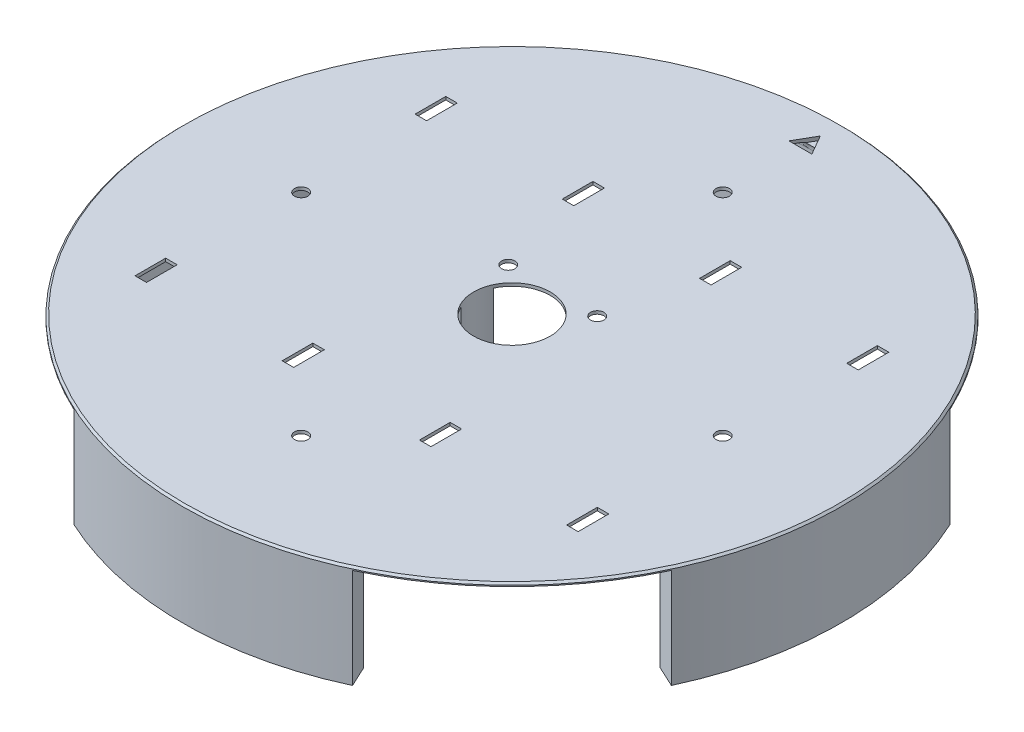
SolidWorks part; units mm, degrees
ref_plane "Ebene vorne" through (0, 0, 0) normal (0, 0, 1) x (1, 0, 0)
ref_plane "Ebene oben" through (0, 0, 0) normal (0, 1, 0) x (1, 0, 0)
ref_plane "Ebene rechts" through (0, 0, 0) normal (1, 0, 0) x (0, 0, -1)
sketch "Skizze1" plane through (0, 0, 0) normal (0, 1, 0) x (1, 0, 0)
  circle A0 centre (0, 0) radius 86
  dimension "D1" = 172
extrude "Aufsatz-Linear austragen1" add sketch "Skizze1" along normal blind 0.8
sketch "Skizze2" plane through (0, 0, 0) normal (0, -1, 0) x (1, 0, 0)
  line L0 (0, 0) -> (0, 86) construction
  line L1 (-36.3452, 77.9425) -> (-33.8095, 72.5046)
  line L2 (0, 0) -> (-36.3452, 77.9425) construction
  line L3 (36.3452, 77.9425) -> (33.8095, 72.5046)
  arc A2 (36.3452, 77.9425) -> (-36.3452, 77.9425) centre (0, 0) ccw
  arc A3 (33.8095, 72.5046) -> (-33.8095, 72.5046) centre (0, 0) ccw
  circle A9 centre (0, 0) radius 86 construction
  dimension "D2" = 6
  dimension "D1" = 25
extrude "Aufsatz-Linear austragen2" add sketch "Skizze2" along normal up to surface (26 mm away)
pattern_circular "Kreismuster1" count 4 over 360 about axis through (0, -99.9325, 0) along (0, 1, 0) of "Aufsatz-Linear austragen2"
sketch "Skizze4" plane through (0, 0, 0) normal (0, -1, 0) x (1, 0, 0)
  circle A0 centre (0, 0) radius 10
extrude "Schnitt-Linear austragen1" cut sketch "Skizze4" against normal up to next
sketch "Skizze7" plane through (0, 0, 0) normal (0, -1, 0) x (1, 0, 0)
  line L0 (-72.5046, 33.8095) -> (0, 0)
  line L1 (0, 0) -> (-72.5046, -33.8095)
  line L2 (0, 0) -> (72.5046, 33.8095)
  line L3 (0, 0) -> (72.5046, -33.8095)
  circle A0 centre (0, 0) radius 10 construction
  circle A1 centre (0, 0) radius 10
  circle A2 centre (0, 0) radius 13
  circle M1 centre (0, 0) radius 10
  dimension "D1" = 3
extrude "Aufsatz-Linear austragen5" add sketch "Skizze7" along normal up to surface (26 mm away) contours L0 A2 L1 M1 | L3 A2 L2 M1
sketch "Skizze6" plane through (0, -26, 0) normal (0, -1, 0) x (1, 0, 0)
  circle A0 centre (-21.4561, 80.0752) radius 1.35
  circle A2 centre (21.4561, 80.0752) radius 1.35
  dimension "D1" = 2.7
extrude "Schnitt-Linear austragen2" cut sketch "Skizze6" against normal blind 10
pattern_circular "Kreismuster2" count 4 over 360 about axis through (0, 0, 0) along (0, 1, 0) of "Schnitt-Linear austragen2"
fillet "Verrundung3" radius 3 6 edges at (0, 0, -80) (80, 0, 0) (0, 0, 80) (-80, 0, 0) (13, 0, 0) (-13, 0, 0)
sketch "Skizze10" plane through (0, 0, 0) normal (0, -1, 0) x (1, 0, 0)
  line L0 (-69.7857, 32.5416) -> (-69.7857, -32.5416) construction
  line L1 (-69.7857, 32.5416) -> (69.7857, 32.5416) construction
  line L2 (-69.7857, -32.5416) -> (69.7857, -32.5416) construction
  line L3 (69.7857, 32.5416) -> (69.7857, -32.5416) construction
  line L4 (57.8126, 32.5416) -> (54.8126, 32.5416)
  line L5 (57.8126, 32.5416) -> (57.8126, 40.5416)
  line L6 (54.8126, 32.5416) -> (54.8126, 40.5416)
  line L7 (57.8126, 40.5416) -> (54.8126, 40.5416)
  line L8 (-86, 0) -> (86, 0) construction
  line L9 (57.6126, -63.9727) -> (57.6126, 64.0273) construction
  line L10 (37.1126, 64.0273) -> (37.1126, -63.9727) construction
  line L11 (45.6126, 64.0273) -> (28.6126, 64.0273) construction
  line L12 (0, 86) -> (0, -86) construction
  line L13 (19.4126, 32.5416) -> (19.4126, 40.5416)
  line L14 (16.4126, 40.5416) -> (19.4126, 40.5416)
  line L15 (16.4126, 32.5416) -> (16.4126, 40.5416)
  line L16 (16.4126, 32.5416) -> (19.4126, 32.5416)
  line L17 (-19.4126, 32.5416) -> (-19.4126, 40.5416)
  line L18 (-16.4126, 40.5416) -> (-19.4126, 40.5416)
  line L19 (-16.4126, 32.5416) -> (-16.4126, 40.5416)
  line L20 (-16.4126, 32.5416) -> (-19.4126, 32.5416)
  line L21 (-57.8126, 40.5416) -> (-54.8126, 40.5416)
  line L22 (-57.8126, 32.5416) -> (-57.8126, 40.5416)
  line L23 (-57.8126, 32.5416) -> (-54.8126, 32.5416)
  line L24 (-54.8126, 32.5416) -> (-54.8126, 40.5416)
  line L25 (57.8126, -40.5416) -> (54.8126, -40.5416)
  line L26 (54.8126, -32.5416) -> (54.8126, -40.5416)
  line L27 (57.8126, -32.5416) -> (57.8126, -40.5416)
  line L28 (57.8126, -32.5416) -> (54.8126, -32.5416)
  line L29 (16.4126, -32.5416) -> (19.4126, -32.5416)
  line L30 (16.4126, -32.5416) -> (16.4126, -40.5416)
  line L31 (16.4126, -40.5416) -> (19.4126, -40.5416)
  line L32 (19.4126, -32.5416) -> (19.4126, -40.5416)
  line L33 (-16.4126, -32.5416) -> (-19.4126, -32.5416)
  line L34 (-16.4126, -32.5416) -> (-16.4126, -40.5416)
  line L35 (-16.4126, -40.5416) -> (-19.4126, -40.5416)
  line L36 (-19.4126, -32.5416) -> (-19.4126, -40.5416)
  line L37 (-54.8126, -32.5416) -> (-54.8126, -40.5416)
  line L38 (-57.8126, -32.5416) -> (-54.8126, -32.5416)
  line L39 (-57.8126, -32.5416) -> (-57.8126, -40.5416)
  line L40 (-57.8126, -40.5416) -> (-54.8126, -40.5416)
  arc A0 (-77.9425, 36.3452) -> (-77.9425, -36.3452) centre (0, 0) ccw construction
  arc A1 (77.9425, -36.3452) -> (77.9425, 36.3452) centre (0, 0) ccw construction
  arc A2 (36.3452, 77.9425) -> (-36.3452, 77.9425) centre (0, 0) ccw construction
  arc A3 (-36.3452, -77.9425) -> (36.3452, -77.9425) centre (0, 0) ccw construction
  dimension "D1" = 3
  dimension "D2" = 0.2
  dimension "D3" = 8
extrude "Schnitt-Linear austragen4" cut sketch "Skizze10" against normal up to next
chamfer "Fase1" distance 0.5 angle 45 1 edges at (0, 0.8, 86)
sketch "Skizze11" plane through (0, 0.8, 0) normal (0, 1, 0) x (1, 0, 0)
  line L0 (0, 80.4641) -> (0, 0) construction
  line L1 (3, 75.2679) -> (0, 80.4641)
  line L2 (0, 80.4641) -> (-3, 75.2679)
  line L3 (-3, 75.2679) -> (3, 75.2679)
  line L4 (0, 80.4641) -> (0, 85.5) construction
  circle A0 centre (0, 77) radius 1.7321 construction
  circle A1 centre (0, 0) radius 85.5 construction
  arc A3 (32.5416, 69.7857) -> (-32.5416, 69.7857) centre (0, 0) ccw construction
  dimension "D1" = 6
extrude "Schnitt-Linear austragen5" cut sketch "Skizze11" against normal blind 1
sketch "Skizze12" plane through (0, 0, 0) normal (0, -1, 0) x (1, 0, 0)
  circle A0 centre (-55, 0) radius 1.75
  circle A1 centre (0, -55) radius 1.75
  circle A2 centre (55, 0) radius 1.75
  circle A3 centre (0, 55) radius 1.75
  circle A4 centre (-11.6052, -10.6442) radius 1.75
  circle A5 centre (11.6052, -10.6442) radius 1.75
  dimension "D1" = 3.5
extrude "Schnitt-Linear austragen6" cut sketch "Skizze12" against normal blind 5
sketch "Skizze13" plane through (0, 0.8, 0) normal (0, 1, 0) x (1, 0, 0)
  line L1 (-54.8126, 40.5416) -> (-19.4126, 40.5416)
  line L2 (-54.8126, 40.5416) -> (-54.8126, 32.5416)
  line L3 (-54.8126, 32.5416) -> (-19.4126, 32.5416)
  line L4 (-19.4126, 40.5416) -> (-19.4126, 32.5416)
  line L5 (-54.8126, -32.5416) -> (-19.4126, -32.5416)
  line L6 (-54.8126, -32.5416) -> (-54.8126, -40.5416)
  line L7 (-54.8126, -40.5416) -> (-19.4126, -40.5416)
  line L8 (-19.4126, -32.5416) -> (-19.4126, -40.5416)
  line L9 (19.4126, -32.5416) -> (54.8126, -32.5416)
  line L10 (19.4126, -32.5416) -> (19.4126, -40.5416)
  line L11 (19.4126, -40.5416) -> (54.8126, -40.5416)
  line L12 (54.8126, -32.5416) -> (54.8126, -40.5416)
  line L13 (19.4126, 40.5416) -> (54.8126, 40.5416)
  line L14 (19.4126, 40.5416) -> (19.4126, 32.5416)
  line L15 (19.4126, 32.5416) -> (54.8126, 32.5416)
  line L16 (54.8126, 40.5416) -> (54.8126, 32.5416)
